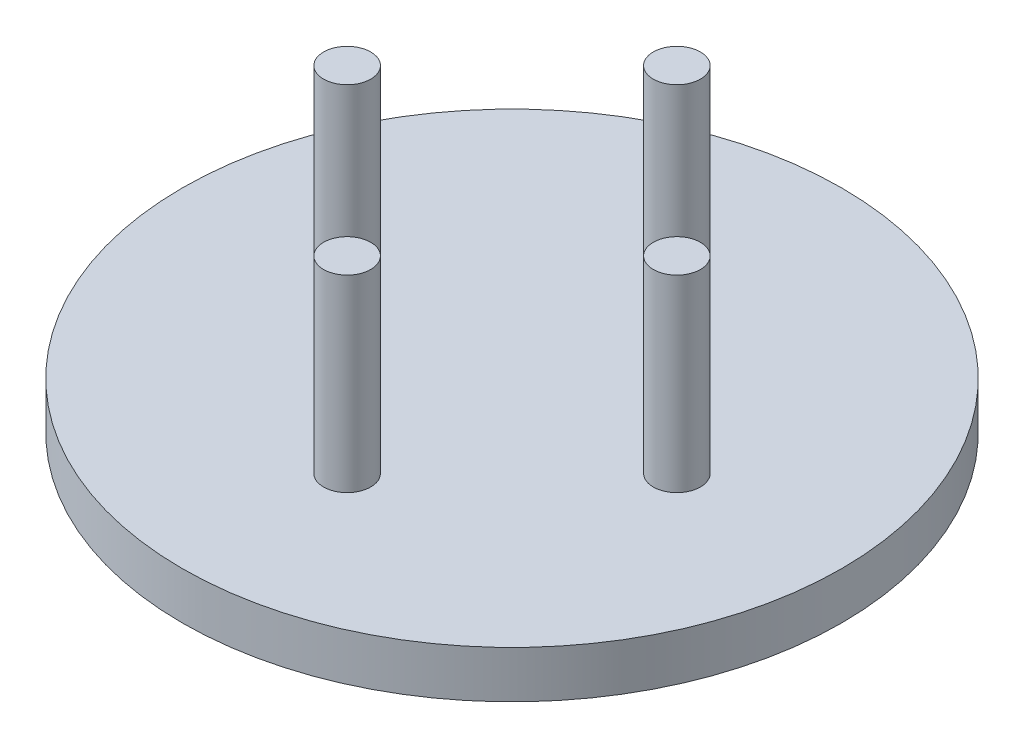
SolidWorks part; units mm, degrees
material "6061 Alloy"
ref_plane "Front Plane" through (0, 0, 0) normal (0, 0, 1) x (1, 0, 0)
ref_plane "Top Plane" through (0, 0, 0) normal (0, 1, 0) x (1, 0, 0)
ref_plane "Right Plane" through (0, 0, 0) normal (1, 0, 0) x (0, 0, -1)
sketch "Sketch1" plane through (0, 0, 0) normal (0, 1, 0) x (1, 0, 0)
  circle A0 centre (0, 0) radius 177.8
extrude "Boss-Extrude1" add sketch "Sketch1" along normal mid plane 25.4
sketch "Sketch2" plane through (0, 12.7, 0) normal (0, 1, 0) x (1, 0, 0)
  circle A0 centre (0, 88.9) radius 12.7
  circle A1 centre (0, -88.9) radius 12.7
  circle A2 centre (88.9, 0) radius 12.7
  circle A3 centre (-88.9, 0) radius 12.7
  dimension "D1" = 88.9
  dimension "D2" = 88.9
  dimension "D3" = 88.9
  dimension "D4" = 88.9
extrude "Boss-Extrude2" add sketch "Sketch2" along normal blind 101.6
